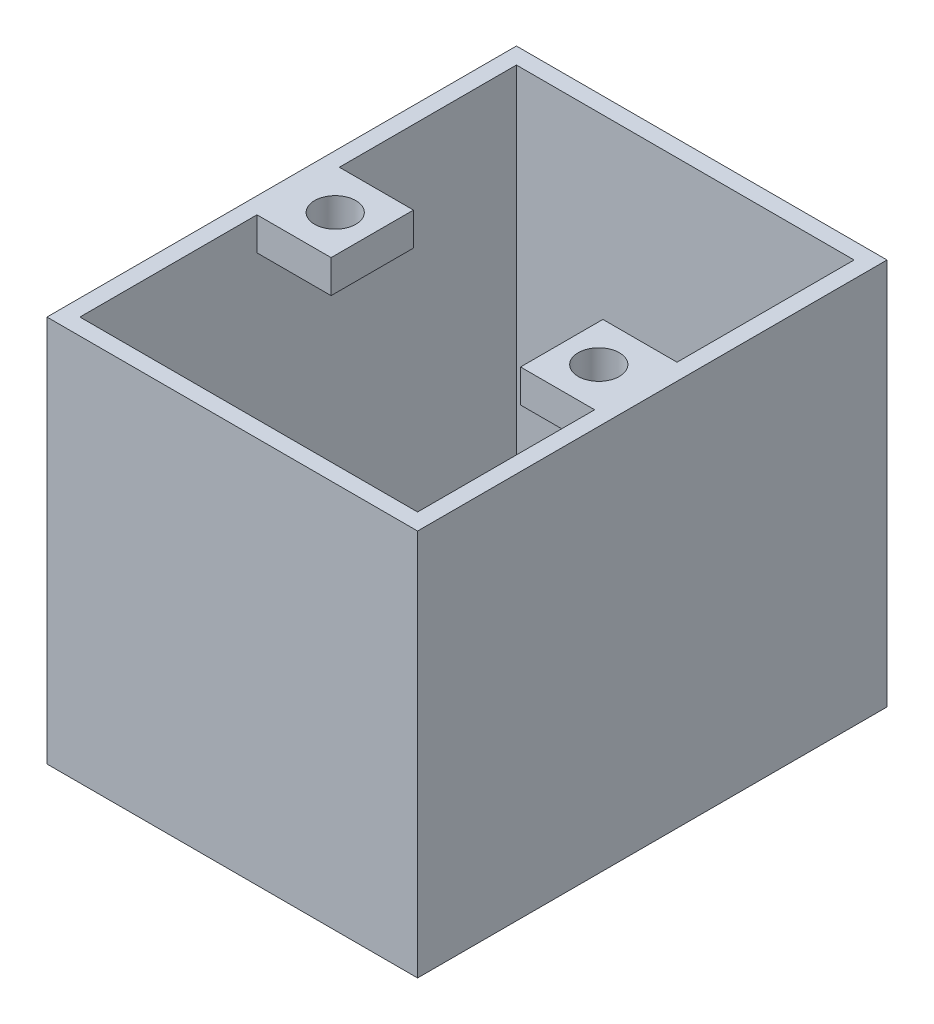
SolidWorks part; units mm, degrees
ref_plane "Plan de face" through (0, 0, 0) normal (0, 0, 1) x (1, 0, 0)
ref_plane "Plan de dessus" through (0, 0, 0) normal (0, 1, 0) x (1, 0, 0)
ref_plane "Plan de droite" through (0, 0, 0) normal (1, 0, 0) x (0, 0, -1)
sketch "Esquisse1" plane through (0, 0, 0) normal (0, 1, 0) x (1, 0, 0)
  line L0 (0, 43) -> (0, 50) construction
  line L1 (0, 0) -> (23, 0)
  line L2 (0, 0) -> (0, 43)
  line L3 (0, 43) -> (23, 43)
  line L4 (23, 0) -> (23, 43)
  line L5 (0, 0) -> (0, -7) construction
  line L6 (23, 16.1381) -> (34, 16.1381) construction
  line L7 (0, 0) -> (-11, 0) construction
  line L9 (-11, 50) -> (34, 50)
  line L10 (-11, 50) -> (-11, -7)
  line L11 (-11, -7) -> (34, -7)
  line L12 (34, 50) -> (34, -7)
  dimension "D1" = 23
  dimension "D2" = 43
  dimension "D3" = 7
  dimension "D4" = 7
  dimension "D5" = 11
  dimension "D6" = 11
extrude "Boss.-Extru.1" add sketch "Esquisse1" along normal blind 2
sketch "Esquisse2" plane through (0, 2, 0) normal (0, 1, 0) x (1, 0, 0)
  line L0 (-11, 50) -> (-9, 50) construction
  line L1 (-11, 50) -> (34, 50)
  line L2 (-11, 50) -> (-11, -7)
  line L3 (-11, -7) -> (34, -7)
  line L4 (34, 50) -> (34, -7)
  line L5 (-9, 50) -> (-9, 48) construction
  line L6 (34, -7) -> (34, -5) construction
  line L7 (34, -5) -> (32, -5) construction
  line L9 (-9, 48) -> (32, 48)
  line L10 (-9, 48) -> (-9, -5)
  line L11 (-9, -5) -> (32, -5)
  line L12 (32, 48) -> (32, -5)
  dimension "D1" = 2
  dimension "D2" = 2
  dimension "D3" = 2
  dimension "D4" = 2
extrude "Boss.-Extru.2" add sketch "Esquisse2" along normal blind 45
sketch "Esquisse3" plane through (0, 47, 0) normal (0, 1, 0) x (1, 0, 0)
  line L0 (-9, 48) -> (-9, -5) construction
  line L1 (-9, -5) -> (-9, 21.5) construction
  line L2 (-9, 21.5) -> (-9, 26.5) construction
  line L3 (-9, 26.5) -> (-9, 16.5) construction
  line L4 (-9, 26.5) -> (32, 26.5) construction
  line L5 (32, -5) -> (32, 48) construction
  line L6 (-9, 16.5) -> (32, 16.5) construction
  line L7 (-9, 26.5) -> (0, 26.5) construction
  line L8 (0, 26.5) -> (0, 16.5) construction
  line L9 (0, 16.5) -> (-9, 16.5) construction
  line L10 (32, 16.5) -> (23, 16.5) construction
  line L11 (-9, 26.5) -> (0, 26.5)
  line L12 (-9, 26.5) -> (-9, 16.5)
  line L13 (-9, 16.5) -> (0, 16.5)
  line L14 (0, 26.5) -> (0, 16.5)
  line L15 (23, 16.5) -> (23, 26.5) construction
  line L16 (23, 26.5) -> (32, 26.5) construction
  line L17 (-9, 16.5) -> (0, 26.5) construction
  line L18 (23, 26.5) -> (32, 26.5)
  line L19 (23, 26.5) -> (23, 16.5)
  line L20 (23, 16.5) -> (32, 16.5)
  line L21 (32, 26.5) -> (32, 16.5)
  line L22 (23, 26.5) -> (32, 16.5) construction
  line L23 (32, 16.5) -> (31.9075, 16.4679) construction
  circle A0 centre (-4.5, 21.5) radius 2.5
  circle A1 centre (27.5, 21.5) radius 2.5
  dimension "D4" = 5
  dimension "D5" = 5
  dimension "D1" = 5
  dimension "D2" = 10
  dimension "D3" = 9
extrude "Boss.-Extru.3" add sketch "Esquisse3" against normal blind 4
